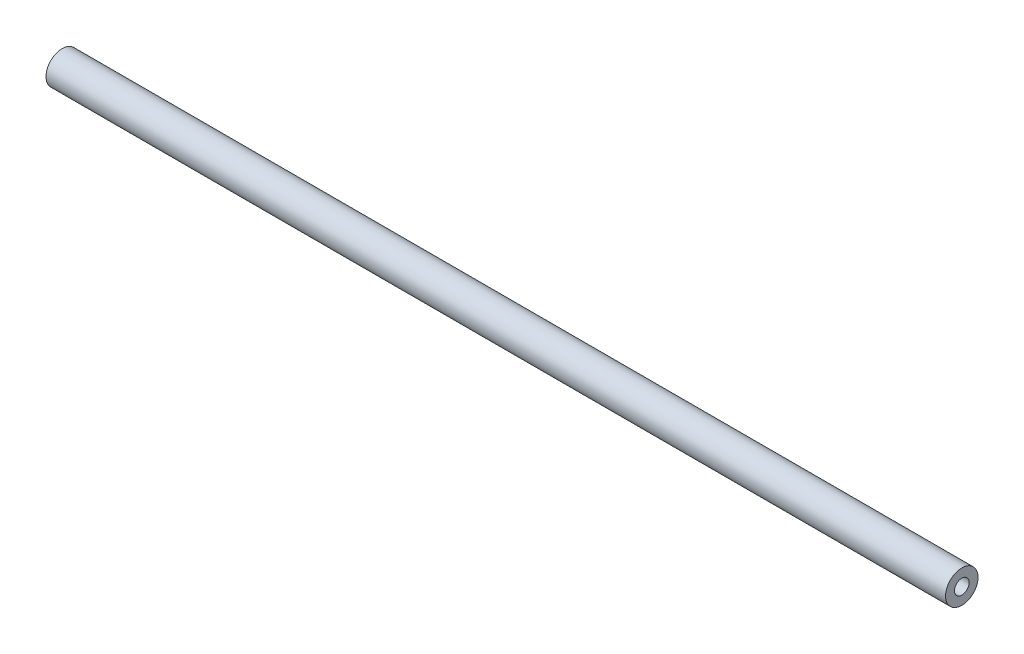
SolidWorks part; units mm, degrees
material "AISI Type A2 Tool Steel"
ref_plane "Front Plane" through (0, 0, 0) normal (0, 0, 1) x (1, 0, 0)
ref_plane "Top Plane" through (0, 0, 0) normal (0, 1, 0) x (1, 0, 0)
ref_plane "Right Plane" through (0, 0, 0) normal (1, 0, 0) x (0, 0, -1)
sketch "Sketch1" plane through (0, 0, 0) normal (0, 0, 1) x (1, 0, 0)
  line L0 (-686.6124, 12.6401) -> (0, 12.6401) construction
  line L1 (0, 12.6401) -> (0, 0) construction
  line L3 (-613.42, 16.9451) -> (-591.2862, 16.9451)
  line L4 (-613.42, 22.1651) -> (-85.58, 22.1651)
  line L5 (-613.42, 22.1651) -> (-613.42, 16.9451)
  line L6 (-588.8008, 12.6401) -> (-110.1992, 12.6401)
  line L7 (-85.58, 22.1651) -> (-85.58, 16.9451)
  line L8 (-591.2862, 16.9451) -> (-588.8008, 12.6401)
  line L9 (-85.58, 16.9451) -> (-107.7138, 16.9451)
  line L10 (-107.7138, 16.9451) -> (-110.1992, 12.6401)
  line L13 (-613.5062, 12.6401) -> (-610.1, 12.6401) construction
  line L14 (-613.42, 3.1151) -> (-613.42, 22.1651) construction
  line L15 (-85.58, 22.1651) -> (-85.58, 3.1151) construction
  dimension "D1" = 19.05
  dimension "D2" = 60
  dimension "D3" = 60
revolve "Revolve1" add sketch "Sketch1" angle 360 about L0
